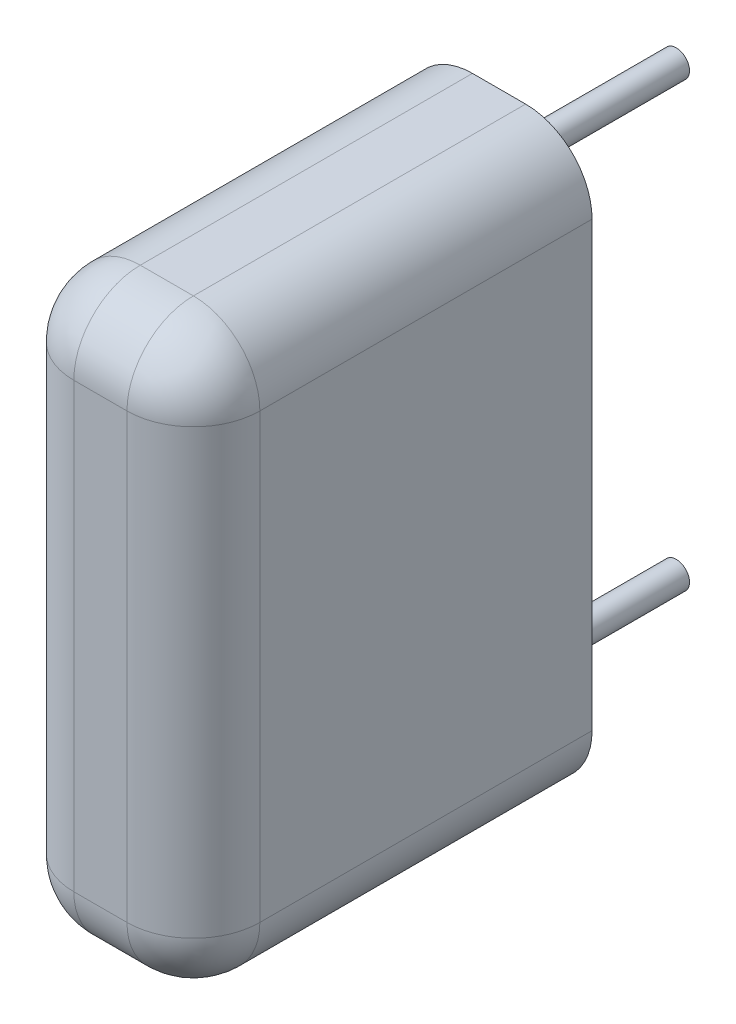
SolidWorks part; units mm, degrees
ref_plane "Спереди" through (0, 0, 0) normal (0, 0, 1) x (1, 0, 0)
ref_plane "Сверху" through (0, 0, 0) normal (0, 1, 0) x (1, 0, 0)
ref_plane "Справа" through (0, 0, 0) normal (1, 0, 0) x (0, 0, -1)
sketch "Эскиз2" plane through (0, 0, 0) normal (0, 0, 1) x (1, 0, 0)
  line L0 (0, 1.5) -> (0, -11.5) construction
  line L1 (-2.1, 1.5) -> (2.1, 1.5)
  line L2 (-2.1, 1.5) -> (-2.1, -11.5)
  line L3 (-2.1, -11.5) -> (2.1, -11.5)
  line L4 (2.1, 1.5) -> (2.1, -11.5)
  point P6 (0, 0)
  dimension "D1" = 13
  dimension "D2" = 4.2
  dimension "D3" = 1.5
extrude "Бобышка-Вытянуть1" add sketch "Эскиз2" along normal blind 9
sketch "Эскиз3" plane through (0, 0, 0) normal (0, 0, -1) x (-1, 0, 0)
  circle A0 centre (0, 0) radius 0.3
  circle A1 centre (0, -10) radius 0.3
  dimension "D1" = 0.6
  dimension "D2" = 10
extrude "Бобышка-Вытянуть2" add sketch "Эскиз3" along normal blind 4
fillet "Скругление1" radius 1.5 8 edges at (0, 1.5, 9) (2.1, -5, 9) (0, -11.5, 9) (-2.1, -5, 9) (2.1, -11.5, 4.5) (-2.1, -11.5, 4.5) (-2.1, 1.5, 4.5) (2.1, 1.5, 4.5)
